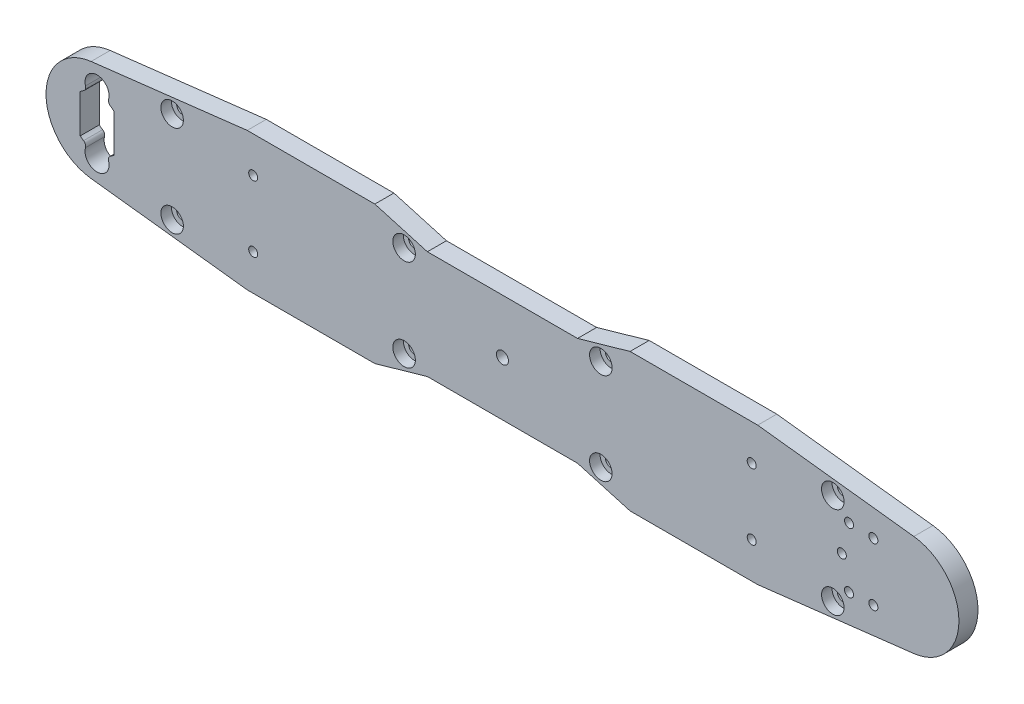
SolidWorks part; units mm, degrees
ref_plane "Alzado" through (0, 0, 0) normal (0, 0, 1) x (1, 0, 0)
ref_plane "Planta" through (0, 0, 0) normal (0, 1, 0) x (1, 0, 0)
ref_plane "Vista lateral" through (0, 0, 0) normal (1, 0, 0) x (0, 0, -1)
sketch "Croquis1" plane through (0, 0, 0) normal (0, 0, 1) x (1, 0, 0)
  line L0 (0, 0) -> (270, 0) construction
  line L1 (135, 0) -> (135, 23) construction
  line L2 (135, 23) -> (50, 23) construction
  line L3 (50, 23) -> (-1.9864, 16.8835)
  line L4 (0, 0) -> (0, -17) construction
  line L5 (50, 23) -> (50, 0) construction
  line L6 (50, 23) -> (92.5, 23)
  line L7 (92.5, 23) -> (110, 18)
  line L8 (110, 18) -> (160, 18)
  line L9 (110, -18) -> (160, -18)
  line L10 (92.5, -23) -> (110, -18)
  line L11 (50, -23) -> (92.5, -23)
  line L12 (50, -23) -> (-1.9864, -16.8835)
  line L13 (177.5, 23) -> (160, 18)
  line L14 (220, 23) -> (177.5, 23)
  line L15 (177.5, -23) -> (160, -18)
  line L16 (220, -23) -> (177.5, -23)
  line L17 (220, -23) -> (271.9864, -16.8835)
  line L18 (220, 23) -> (271.9864, 16.8835)
  line L19 (45, 10) -> (225, 10) construction
  line L20 (45, -10) -> (225, -10) construction
  circle A0 centre (0, 0) radius 17
  circle A1 centre (270, 0) radius 17
  circle A2 centre (0, 0) radius 35 construction
  circle A3 centre (45, 0) radius 10 construction
  circle A4 centre (225, 0) radius 10 construction
  point P20 (135, 18)
  point P23 (135, -18)
  point P35 (135, -10)
  point P38 (135, 10)
  dimension "D2" = 34
  dimension "D7" = 70
  dimension "D8" = 20
  dimension "D1" = 270
  dimension "D3" = 23
  dimension "D4" = 50
  dimension "D5" = 5
  dimension "D6" = 25
extrude "Saliente-Extruir1" add sketch "Croquis1" along normal blind 6.35 contours A0 | A1 L18 L14 L13 L8 L7 L6 L3 A0 L12 L11 L10 L9 L15 L16 L17 L19 A4 L20 A3 | A1
sketch "Croquis2" plane through (0, 0, 6.35) normal (0, 0, 1) x (1, 0, 0)
  line L0 (0, 0) -> (270, 0) construction
  line L1 (0, 0) -> (0, 10) construction
  line L2 (-5.6, 6.3945) -> (-5.6, -6.3945)
  line L3 (5.6, 6.3945) -> (5.6, -6.3945)
  circle A0 centre (0, 0) radius 8.5
  circle A1 centre (0, 10) radius 4
  circle A2 centre (0, -10) radius 4
  dimension "D1" = 17
  dimension "D4" = 8
  dimension "D2" = 5.6
  dimension "D3" = 10
sketch "Croquis3" plane through (0, 0, 6.35) normal (0, 0, 1) x (1, 0, 0)
  line L0 (0, 0) -> (270, 0) construction
  line L1 (135, 0) -> (135, 18) construction
  line L2 (110, 18) -> (160, 18) construction
  line L3 (52, 0) -> (52, 11) construction
  circle A0 centre (52, 11) radius 1.5
  circle A1 centre (52, -11) radius 1.5
  circle A2 centre (218, -11) radius 1.5
  circle A3 centre (218, 11) radius 1.5
  circle A4 centre (135, 0) radius 2
  dimension "D2" = 3
  dimension "D4" = 4
  dimension "D1" = 11
  dimension "D3" = 83
extrude "Cortar-Extruir2" cut sketch "Croquis3" against normal through all
extrude "Cortar-Extruir3" cut sketch "Croquis2" against normal blind 56 contours A0 A1 | A0 A1 | A0 A2 L3 A1 L2 | A2 A0 | A2 A0
fillet "Redondeo2" radius 1.5 4 edges at (-3.3489, -7.8125, 3.175) (3.3489, -7.8125, 3.175) (3.3489, 7.8125, 3.175) (-3.3489, 7.8125, 3.175)
sketch "Croquis5" plane through (0, 0, 6.35) normal (0, 0, 1) x (1, 0, 0)
  line L0 (0, 0) -> (270, 0) construction
  line L1 (25, -15.2633) -> (245, -15.2633) construction
  line L2 (135, 0) -> (135, 18) construction
  line L3 (110, 18) -> (160, 18) construction
  line L4 (50, 23) -> (-1.9864, 16.8835) construction
  line L5 (25, 20.0258) -> (102.9098, 20.0258) construction
  line L6 (92.5, 23) -> (110, 18) construction
  line L7 (50, 23) -> (92.5, 23) construction
  line L8 (92.5, -23) -> (110, -18) construction
  circle A0 centre (25, 15.2633) radius 4.7625 construction
  circle A2 centre (25, 15.2633) radius 2
  circle A3 centre (25, -15.2633) radius 2
  circle A4 centre (245, -15.2633) radius 2
  circle A5 centre (245, 15.2633) radius 2
  circle A6 centre (245, -15.2633) radius 2
  circle A7 centre (245, 15.2633) radius 2
  circle A8 centre (102.2428, -15.2633) radius 4.7625 construction
  circle A9 centre (102.2428, -15.2633) radius 2
  circle A10 centre (102.2428, 15.2633) radius 2
  circle A11 centre (167.7572, -15.2633) radius 2
  circle A12 centre (167.7572, 15.2633) radius 2
  dimension "D1" = 9.525
  dimension "D3" = 4
  dimension "D5" = 9.525
  dimension "D6" = 4
  dimension "D2" = 110
  dimension "D4" = 2.9742
extrude "Cortar-Extruir5" cut sketch "Croquis5" against normal through all contours A2 | A3 | A10 | A9 | A11 | A12 | A5 | A4
sketch "Croquis7" plane through (0, 0, 6.35) normal (0, 0, 1) x (1, 0, 0)
  circle A0 centre (25, 15.2633) radius 3.75
  circle A1 centre (25, -15.2633) radius 3.75
  circle A2 centre (245, 15.2633) radius 3.75
  circle A3 centre (245, -15.2633) radius 3.75
  circle A4 centre (102.2428, 15.2633) radius 3.75
  circle A5 centre (102.2428, -15.2633) radius 3.75
  circle A6 centre (167.7572, -15.2633) radius 3.75
  circle A7 centre (167.7572, 15.2633) radius 3.75
  dimension "D1" = 7.5
extrude "Cortar-Extruir6" cut sketch "Croquis7" against normal blind 3.5
sketch "Croquis8" plane through (0, 0, 6.35) normal (0, 0, 1) x (1, 0, 0)
  line L0 (287, 0) -> (270, 0) construction
  line L1 (270, 0) -> (240, 0) construction
  line L3 (270.4475, 13.4926) -> (240, 14.5025) construction
  line L4 (240, 14.5025) -> (240, -14.5025) construction
  line L5 (270, 0) -> (270.4475, 13.4926) construction
  line L6 (270.4475, -13.4926) -> (240, -14.5025) construction
  line L7 (270.3647, 10.994) -> (239.9171, 12.0038) construction
  line L8 (250.3979, 9.9878) -> (270, 0) construction
  line L9 (258.5093, 9.6418) -> (270, 0) construction
  arc A0 (271.9864, -16.8835) -> (271.9864, 16.8835) centre (270, 0) ccw construction
  arc A1 (270.4475, -13.4926) -> (270.4475, 13.4926) centre (270, 0) ccw construction
  circle A2 centre (248, 0) radius 1.5
  circle A3 centre (270, 0) radius 22 construction
  circle A4 centre (270, 0) radius 13.5 construction
  circle A5 centre (250.3979, 9.9878) radius 1.5
  circle A6 centre (258.5093, 9.6418) radius 1.5
  circle A9 centre (258.5093, -9.6418) radius 1.5
  circle A10 centre (250.3979, -9.9878) radius 1.5
  point P16 (240, 0)
  dimension "D1" = 13.5
  dimension "D4" = 3
  dimension "D6" = 44
  dimension "D7" = 27
  dimension "D9" = 27
  dimension "D2" = 29.0049
  dimension "D3" = 30
  dimension "D5" = 88.1
  dimension "D10" = 15
  dimension "D11" = 40
  dimension "D8" = 2.5
extrude "Cortar-Extruir7" cut sketch "Croquis8" against normal through all
